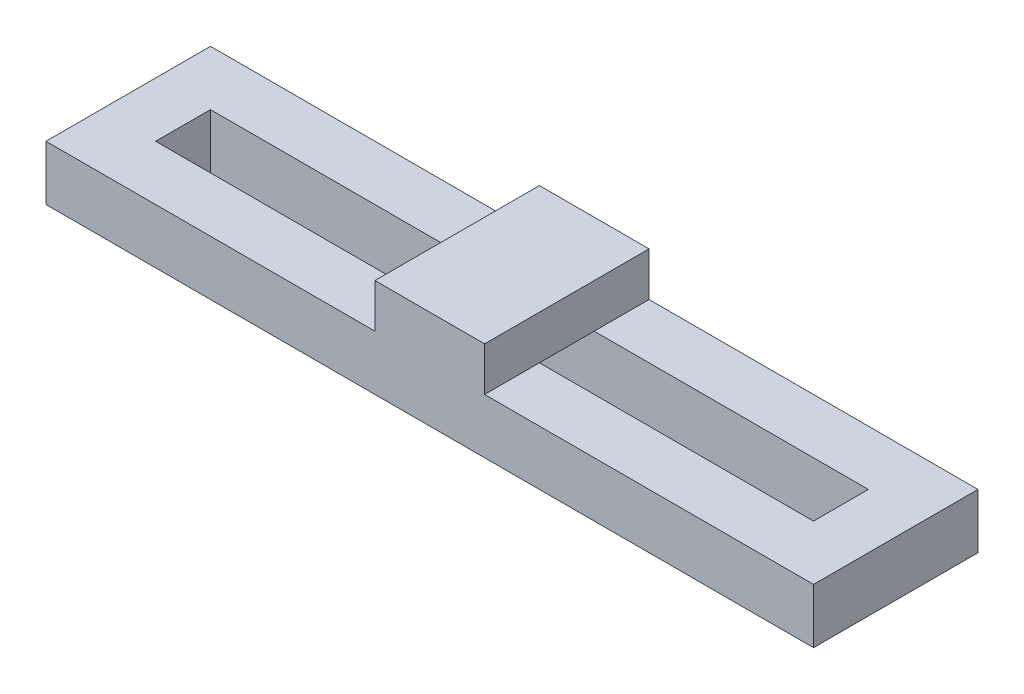
SolidWorks part; units mm, degrees
ref_plane "Front Plane" through (0, 0, 0) normal (0, 0, 1) x (1, 0, 0)
ref_plane "Top Plane" through (0, 0, 0) normal (0, 1, 0) x (1, 0, 0)
ref_plane "Right Plane" through (0, 0, 0) normal (1, 0, 0) x (0, 0, -1)
sketch "Sketch2" plane through (0, 0, 0) normal (0, 1, 0) x (1, 0, 0)
  line L1 (-35, -7.5) -> (35, -7.5)
  line L2 (-35, -7.5) -> (-35, 7.5)
  line L3 (-35, 7.5) -> (35, 7.5)
  line L4 (35, -7.5) -> (35, 7.5)
  line L5 (-35, -7.5) -> (35, 7.5) construction
  line L6 (-35, 7.5) -> (35, -7.5) construction
  line L7 (30, -2.5) -> (-30, -2.5)
  line L8 (30, -2.5) -> (30, 2.5)
  line L9 (30, 2.5) -> (-30, 2.5)
  line L10 (-30, -2.5) -> (-30, 2.5)
  line L11 (30, -2.5) -> (-30, 2.5) construction
  line L12 (30, 2.5) -> (-30, -2.5) construction
  point P0 (0, 0)
  point P6 (0, 0)
  dimension "D1" = 70
  dimension "D2" = 15
  dimension "D3" = 60
  dimension "D4" = 5
extrude "Boss-Extrude3" add sketch "Sketch2" along normal blind 5
sketch "Sketch3" plane through (0, 5, 0) normal (0, 1, 0) x (1, 0, 0)
  line L0 (35, 7.5) -> (-35, 7.5) construction
  line L1 (-5, -7.5) -> (5, -7.5)
  line L2 (-5, -7.5) -> (-5, 7.5)
  line L3 (-5, 7.5) -> (5, 7.5)
  line L4 (5, -7.5) -> (5, 7.5)
  line L5 (-5, -7.5) -> (5, 7.5) construction
  line L6 (-5, 7.5) -> (5, -7.5) construction
  point P0 (0, 0)
  dimension "D1" = 10
extrude "Boss-Extrude4" add sketch "Sketch3" along normal blind 4
ref_plane "Plane1" through (0, 0, 0) normal (0, 0, -1) x (-1, 0, 0)
